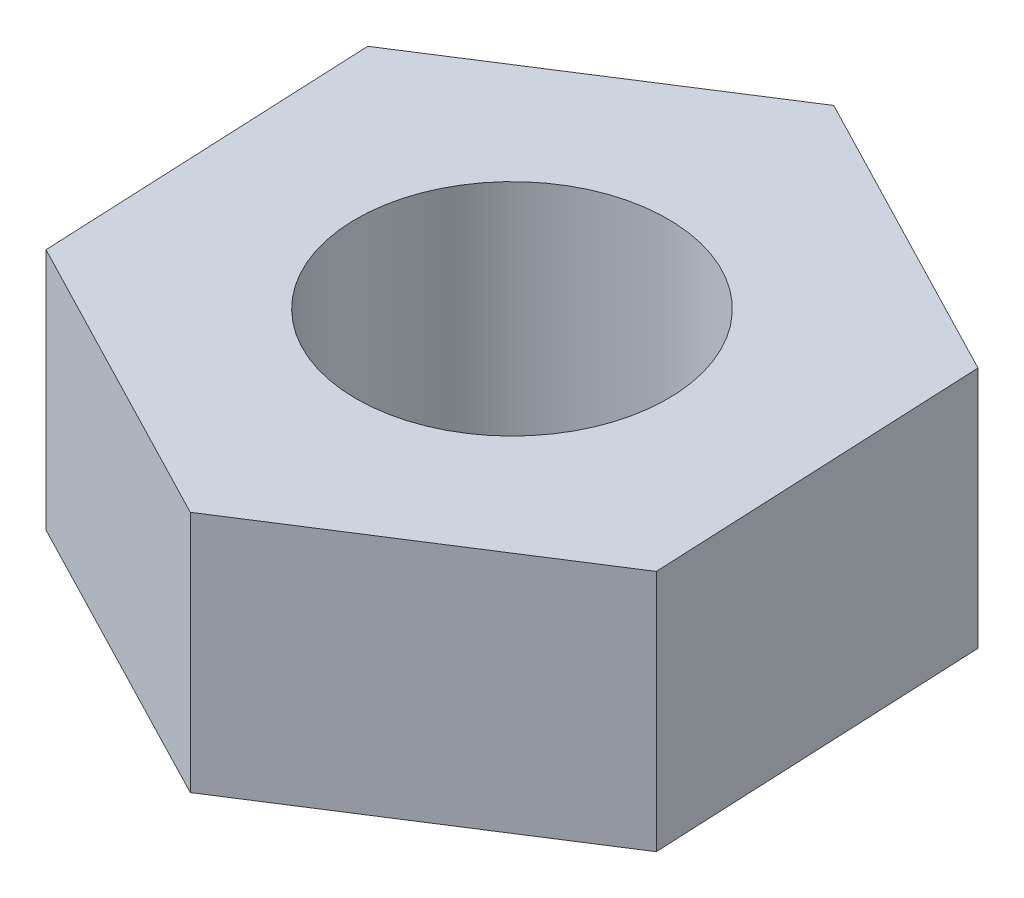
SolidWorks part; units mm, degrees
material "Cast Alloy Steel"
ref_plane "Front Plane" through (0, 0, 0) normal (0, 0, 1) x (1, 0, 0)
ref_plane "Top Plane" through (0, 0, 0) normal (0, 1, 0) x (1, 0, 0)
ref_plane "Right Plane" through (0, 0, 0) normal (1, 0, 0) x (0, 0, -1)
sketch "Sketch1" plane through (0, 0, 0) normal (0, 1, 0) x (1, 0, 0)
  line L1 (4.7422, 3.033) -> (-0.2556, 5.6234)
  line L2 (-0.2556, 5.6234) -> (-4.9978, 2.5904)
  line L3 (-4.9978, 2.5904) -> (-4.7422, -3.033)
  line L4 (-4.7422, -3.033) -> (0.2556, -5.6234)
  line L5 (0.2556, -5.6234) -> (4.9978, -2.5904)
  line L6 (4.9978, -2.5904) -> (4.7422, 3.033)
  circle A0 centre (0, 0) radius 4.875 construction
extrude "Boss-Extrude1" add sketch "Sketch1" along normal mid plane 4.05
sketch "Sketch2" plane through (0, 2.025, 0) normal (0, 1, 0) x (1, 0, 0)
  circle A0 centre (0, 0) radius 2.6
extrude "Cut-Extrude1" cut sketch "Sketch2" against normal up to next
